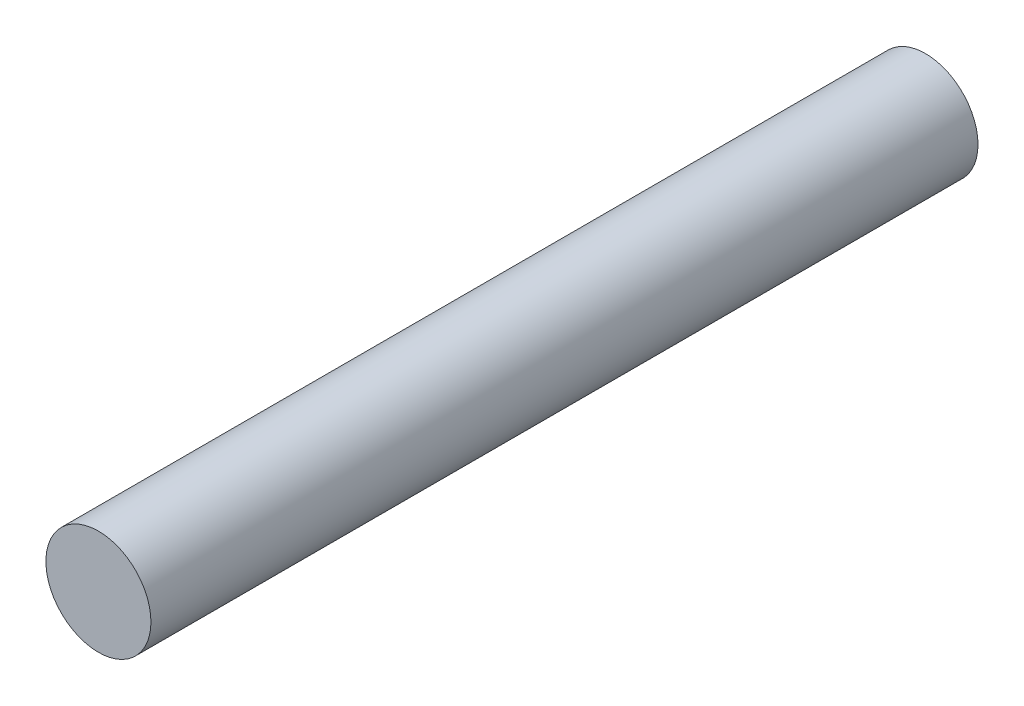
SolidWorks part; units mm, degrees
ref_plane "Alzado" through (0, 0, 0) normal (0, 0, 1) x (1, 0, 0)
ref_plane "Planta" through (0, 0, 0) normal (0, 1, 0) x (1, 0, 0)
ref_plane "Vista lateral" through (0, 0, 0) normal (1, 0, 0) x (0, 0, -1)
sketch "Croquis1" plane through (0, 0, 0) normal (0, 0, 1) x (1, 0, 0)
  circle A0 centre (0, 0) radius 6.35
  dimension "D1" = 12.7
sketch "Croquis2" plane through (0, 0, 0) normal (1, 0, 0) x (0, 0, -1)
  line L0 (0, 0) -> (100, 0)
  dimension "100" = 100
sweep "Barrer1" add profiles "Croquis1" path "Croquis2"
